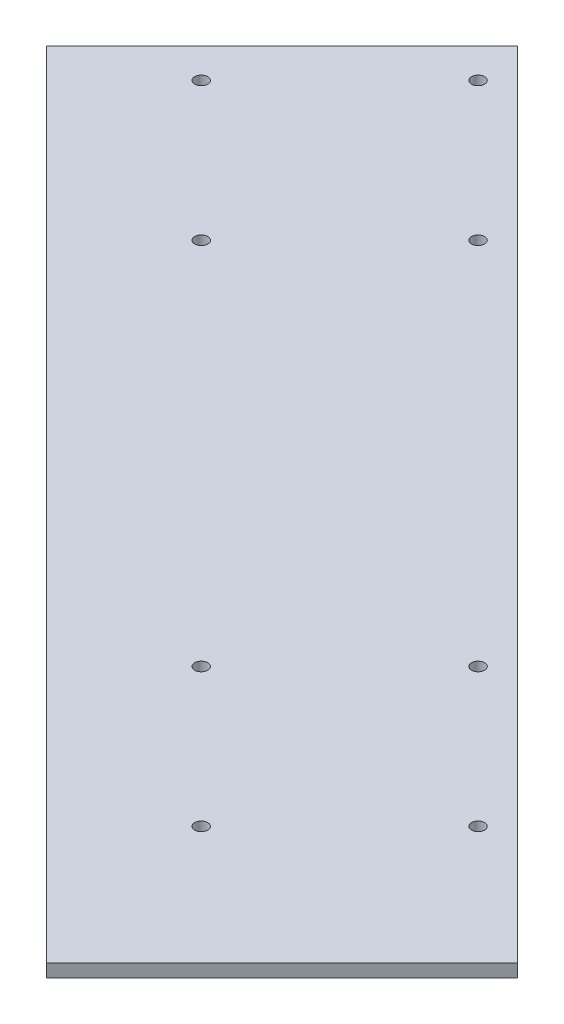
SolidWorks part; units mm, degrees
ref_plane "Alzado" through (0, 0, 0) normal (0, 0, 1) x (1, 0, 0)
ref_plane "Planta" through (0, 0, 0) normal (0, 1, 0) x (1, 0, 0)
ref_plane "Vista lateral" through (0, 0, 0) normal (1, 0, 0) x (0, 0, -1)
sketch "Croquis2" plane through (0, 0, 0) normal (0, 1, 0) x (1, 0, 0)
  line L1 (-650, -500) -> (650, -500)
  line L2 (-650, -500) -> (-650, 500)
  line L3 (-650, 500) -> (650, 500)
  line L4 (650, -500) -> (650, 500)
  line L5 (-650, -500) -> (650, 500) construction
  line L6 (-650, 500) -> (650, -500) construction
  point P0 (0, 0)
  dimension "D1" = 1000
  dimension "D2" = 650
extrude "Saliente-Extruir1" add sketch "Croquis2" along normal blind 10 contours L4 L3 L2 L1
ref_plane "Plano1" through (0, 10, 0) normal (0, 1, 0) x (1, 0, 0)
sketch "Croquis3" plane through (0, 10, 0) normal (0, 1, 0) x (1, 0, 0)
  line L0 (-72.832, -350) -> (-72.832, -500) construction
  line L2 (-650, -500) -> (650, -500) construction
  line L4 (-19.799, -296.967) -> (-650, 333.234) construction
  line L5 (-650, -500) -> (-650, 500) construction
  line L6 (-125.865, -190.901) -> (-72.832, -137.868) construction
  line L7 (-72.832, -137.868) -> (33.234, -243.934) construction
  line L8 (33.234, -243.934) -> (-72.832, -350) construction
  line L9 (-72.832, -350) -> (-178.898, -243.934) construction
  line L10 (-178.898, -243.934) -> (-125.865, -190.901) construction
  line L12 (-514.7737, 198.0078) -> (-567.8067, 144.9747) construction
  line L13 (-567.8067, 144.9747) -> (-461.7407, 38.9087) construction
  line L14 (-461.7407, 38.9087) -> (-355.6747, 144.9747) construction
  line L15 (-355.6747, 144.9747) -> (-461.7407, 251.0408) construction
  line L16 (-461.7407, 251.0408) -> (-514.7737, 198.0078) construction
  circle A0 centre (-72.832, -137.868) radius 5
  circle A1 centre (33.234, -243.934) radius 5
  circle A2 centre (-72.832, -350) radius 5
  circle A3 centre (-178.898, -243.934) radius 5
  circle A4 centre (-461.7407, 251.0408) radius 5
  circle A5 centre (-355.6747, 144.9747) radius 5
  circle A6 centre (-461.7407, 38.9087) radius 5
  circle A7 centre (-567.8067, 144.9747) radius 5
  dimension "D6" = 10
  dimension "D7" = 10
  dimension "D8" = 10
  dimension "D9" = 10
  dimension "D12" = 10
  dimension "D13" = 10
  dimension "D14" = 10
  dimension "D15" = 10
  dimension "D1" = 150
  dimension "D2" = 150
  dimension "D3" = 75
  dimension "D4" = 75
  dimension "D5" = 150
  dimension "D10" = 75
  dimension "D11" = 75
  dimension "D16" = 400
extrude "Cortar-Extruir1" cut sketch "Croquis3" against normal through all
sketch "Croquis5" plane through (0, 0, 0) normal (0, 1, 0) x (1, 0, 0)
  line L0 (0, 0) -> (-500, 500)
  line L1 (-650, 500) -> (650, 500) construction
  line L2 (0, 0) -> (500, -500)
  line L3 (-650, -500) -> (650, -500) construction
  line L4 (-500, 500) -> (650, 500)
  line L5 (650, -500) -> (650, 500) construction
  line L6 (650, 500) -> (650, -500)
  line L7 (650, -500) -> (500, -500)
  line L8 (-41.5417, -500) -> (-650, 108.4583)
  line L9 (-650, -500) -> (-650, 500) construction
  line L10 (-650, 108.4583) -> (-650, -500)
  line L11 (-650, -500) -> (-41.5417, -500)
  dimension "D1" = 45
  dimension "D2" = 45
extrude "Cortar-Extruir2" cut sketch "Croquis5" along normal blind 10
sketch "Croquis6" plane through (0, 0, 0) normal (0, 1, 0) x (1, 0, 0)
  line L0 (-650, 108.4583) -> (-379.2291, 379.2291)
  line L1 (-500, 500) -> (500, -500) construction
  line L2 (-650, 108.4583) -> (-650, 500)
  line L3 (-650, 500) -> (-500, 500)
  line L4 (-500, 500) -> (-379.2291, 379.2291)
  line L5 (-41.5417, -500) -> (229.2291, -229.2291)
  line L6 (229.2291, -229.2291) -> (500, -500)
  line L7 (500, -500) -> (-41.5417, -500)
extrude "Cortar-Extruir3" cut sketch "Croquis6" along normal blind 10
sketch "Sketch1" plane through (0, 10, 0) normal (0, 1, 0) x (1, 0, 0)
  line L0 (-379.2291, 379.2291) -> (-469.383, 289.0752)
  line L1 (-650, 108.4583) -> (-379.2291, 379.2291) construction
  line L2 (-469.383, 289.0752) -> (139.0752, -319.383)
  line L3 (229.2291, -229.2291) -> (-41.5417, -500) construction
  line L4 (139.0752, -319.383) -> (229.2291, -229.2291)
  line L5 (-379.2291, 379.2291) -> (229.2291, -229.2291) construction
  line L6 (229.2291, -229.2291) -> (-379.2291, 379.2291)
  point P11 (0, 0)
  point P12 (-469.383, 289.0752)
extrude "Cut-Extrude1" cut sketch "Sketch1" against normal through all
